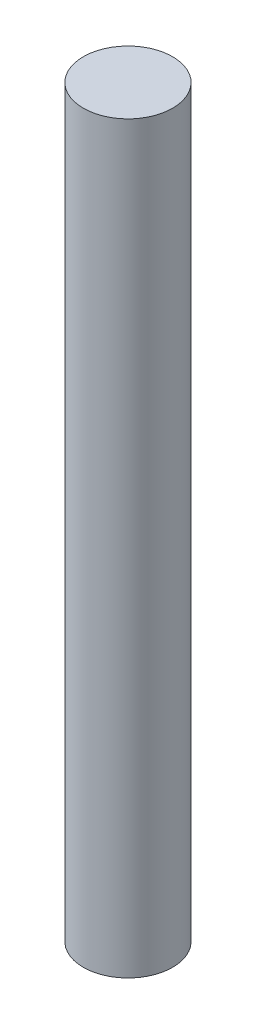
SolidWorks part; units mm, degrees
ref_plane "Front Plane" through (0, 0, 0) normal (0, 0, 1) x (1, 0, 0)
ref_plane "Top Plane" through (0, 0, 0) normal (0, 1, 0) x (1, 0, 0)
ref_plane "Right Plane" through (0, 0, 0) normal (1, 0, 0) x (0, 0, -1)
sketch "Sketch1" plane through (0, 0, 0) normal (0, 1, 0) x (1, 0, 0)
  circle A0 centre (0, 0) radius 6
extrude "Boss-Extrude1" add sketch "Sketch1" along normal blind 100
